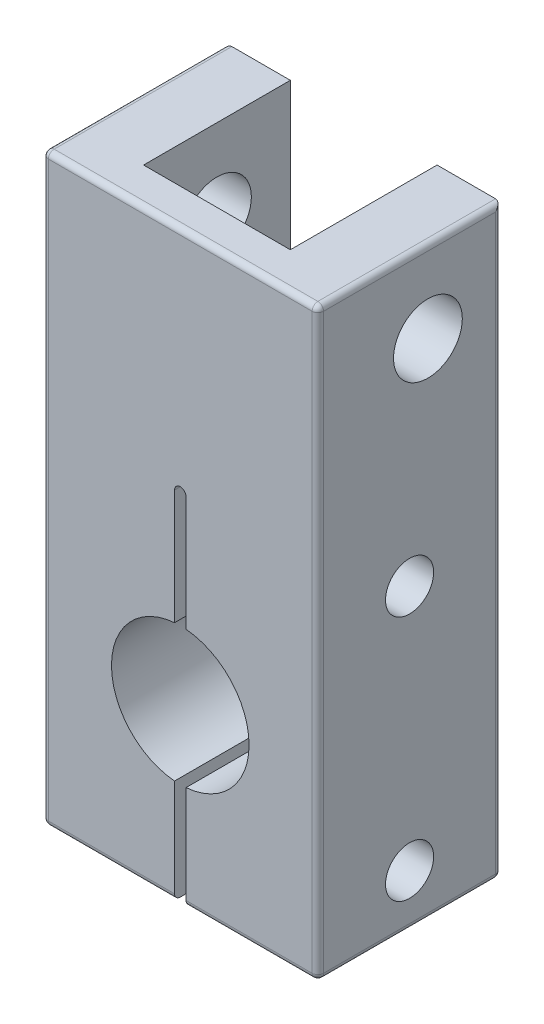
SolidWorks part; units mm, degrees
ref_plane "Plan de face" through (0, 0, 0) normal (0, 0, 1) x (1, 0, 0)
ref_plane "Plan de dessus" through (0, 0, 0) normal (0, 1, 0) x (1, 0, 0)
ref_plane "Plan de droite" through (0, 0, 0) normal (1, 0, 0) x (0, 0, -1)
sketch "Esquisse1" plane through (0, 0, 0) normal (0, 0, 1) x (1, 0, 0)
  line L0 (0, 0) -> (24, 0)
  line L1 (24, 0) -> (24, 24)
  line L3 (24, 24) -> (24, 51)
  line L4 (24, 51) -> (0, 51)
  line L5 (0, 51) -> (0, 30)
  line L7 (0, 30) -> (0, 0)
  line L8 (0, 30) -> (24, 0) construction
  line L9 (0, 0) -> (24, 24) construction
  line L10 (12, 34.8621) -> (12, -29.8966) construction
  circle A0 centre (12, 15) radius 6
  point P16 (12, 15)
  point P17 (12, 0)
  point P18 (0, 15)
  dimension "D1" = 12
  dimension "D2" = 15
  dimension "D3" = 12
  dimension "D5" = 36
extrude "Boss.-Extru.1" add sketch "Esquisse1" along normal blind 16
sketch "Esquisse2" plane through (0, 0, 0) normal (0, 0, -1) x (-1, 0, 0)
  line L0 (-12, 32.8802) -> (-12, 9.6875) construction
  line L1 (-12, 31) -> (-12, -14) construction
  line L2 (-11.5, 31) -> (-11.5, -14)
  line L3 (-12.5, 31) -> (-12.5, -14)
  circle A0 centre (-12, 15) radius 6 construction
  arc A1 (-11.5, 31) -> (-12.5, 31) centre (-12, 31) ccw
  arc A2 (-12.5, -14) -> (-11.5, -14) centre (-12, -14) ccw
  point P0 (-24, 0)
  point P1 (0, 0)
  point P3 (-12, 15)
  point P9 (-12, 8.5)
  dimension "D1" = 1
  dimension "D2" = 16
  dimension "D3" = 45
extrude "Enlèv. mat.-Extru.1" cut sketch "Esquisse2" against normal up to next
sketch "Esquisse4" plane through (24, 0, 0) normal (1, 0, 0) x (0, 0, -1)
  line L0 (-16, 20.9791) -> (0, 20.9791) construction
  line L1 (-16, 51) -> (0, 51) construction
  line L2 (-16, 0) -> (0, 0) construction
  line L3 (-8, 51) -> (-8, 0) construction
  line L4 (-17.5742, 31) -> (8.8694, 31) construction
  line L5 (-16, 31) -> (0, 31) construction
  line L6 (-8, 31) -> (-8, 20.9791) construction
  line L7 (-8, 9.0209) -> (-8, 0) construction
  line L9 (-20.268, 20.9791) -> (17.9758, 20.9791) construction
  line L10 (-18.4982, 9.0209) -> (7.4337, 9.0209) construction
  line L11 (0, 9.0209) -> (-16, 9.0209) construction
  circle A0 centre (-8, 25.9896) radius 2.1
  circle A1 centre (-8, 4.5104) radius 2.1
  point P0 (-8, 0)
  point P1 (-8, 51)
  dimension "D1" = 4.2
  dimension "D2" = 4.2
extrude "Enlèv. mat.-Extru.2" cut sketch "Esquisse4" against normal through all
sketch "Esquisse6" plane through (0, 51, 0) normal (0, 1, 0) x (1, 0, 0)
  line L0 (0, 0) -> (24, -16) construction
  line L3 (0, -16) -> (24, 0) construction
  line L4 (12, 3.2496) -> (12, -18.68) construction
  line L5 (24, 0) -> (0, 0) construction
  line L6 (5.6, 0) -> (18.4, 0)
  line L7 (5.6, 0) -> (5.6, -12.8)
  line L8 (5.6, -12.8) -> (18.4, -12.8)
  line L9 (18.4, 0) -> (18.4, -12.8)
  line L10 (24, 0) -> (0, 0) construction
  point P26 (12, -8)
  dimension "D1" = 12.8
  dimension "D2" = 12.8
extrude "Enlèv. mat.-Extru.3" cut sketch "Esquisse6" against normal blind 15
sketch "Esquisse7" plane through (24, 0, 0) normal (1, 0, 0) x (0, 0, -1)
  line L0 (-16, 51) -> (0, 51) construction
  line L1 (-12.8, 51) -> (0, 51) construction
  line L2 (-6.4, 51) -> (-6.4, 0) construction
  circle A0 centre (-6.4, 43.9) radius 3
  point P0 (-6.4, 51)
  dimension "D1" = 6
  dimension "D2" = 7.1
extrude "Enlèv. mat.-Extru.5" cut sketch "Esquisse7" against normal through all
fillet "Congé1" radius 0.5 13 edges at (0, 51, 8) (0, 25.5, 0) (18.25, 0, 0) (5.75, 0, 0) (0, 0, 8) (5.75, 0, 16) (18.25, 0, 16) (24, 0, 8) (0, 25.5, 16) (24, 25.5, 0) (24, 25.5, 16) (12, 51, 16) (24, 51, 8)
